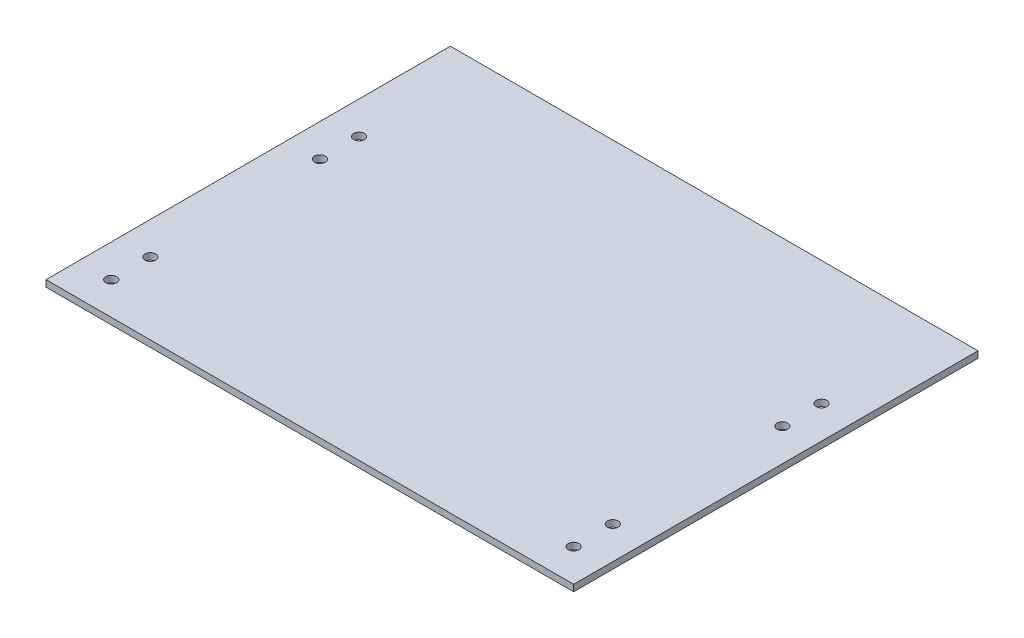
SolidWorks part; units mm, degrees
material "Thornel Mat VMA"
ref_plane "Front Plane" through (0, 0, 0) normal (0, 0, 1) x (1, 0, 0)
ref_plane "Top Plane" through (0, 0, 0) normal (0, 1, 0) x (1, 0, 0)
ref_plane "Right Plane" through (0, 0, 0) normal (1, 0, 0) x (0, 0, -1)
sketch "Sketch1" plane through (0, 0, 0) normal (0, 1, 0) x (1, 0, 0)
  line L0 (-70.9, 26) -> (-70.9, -26) construction
  line L1 (0, 0) -> (-70.9, 0) construction
  line L2 (0, 0) -> (0, 38) construction
  line L3 (80.9, 76) -> (80.9, -48)
  line L9 (-80.9, 76) -> (80.9, 76)
  line L10 (-80.9, 76) -> (-80.9, -48)
  line L11 (-80.9, -48) -> (80.9, -48)
  line L12 (0, 76) -> (0, -48) construction
  circle A0 centre (-70.9, 38) radius 1.65
  circle A1 centre (-70.9, 26) radius 1.65
  circle A2 centre (-70.9, -26) radius 1.65
  circle A3 centre (-70.9, -38) radius 1.65
  circle A4 centre (70.9, 38) radius 1.65
  circle A5 centre (70.9, 26) radius 1.65
  circle A6 centre (70.9, -26) radius 1.65
  circle A7 centre (70.9, -38) radius 1.65
  dimension "D2" = 3.3
  dimension "D1" = 70.9
  dimension "D3" = 12
  dimension "D4" = 2
  dimension "D5" = 64
  dimension "D6" = 10
  dimension "D7" = 10
  dimension "D8" = 124
extrude "Boss-Extrude1" add sketch "Sketch1" along normal blind 2
